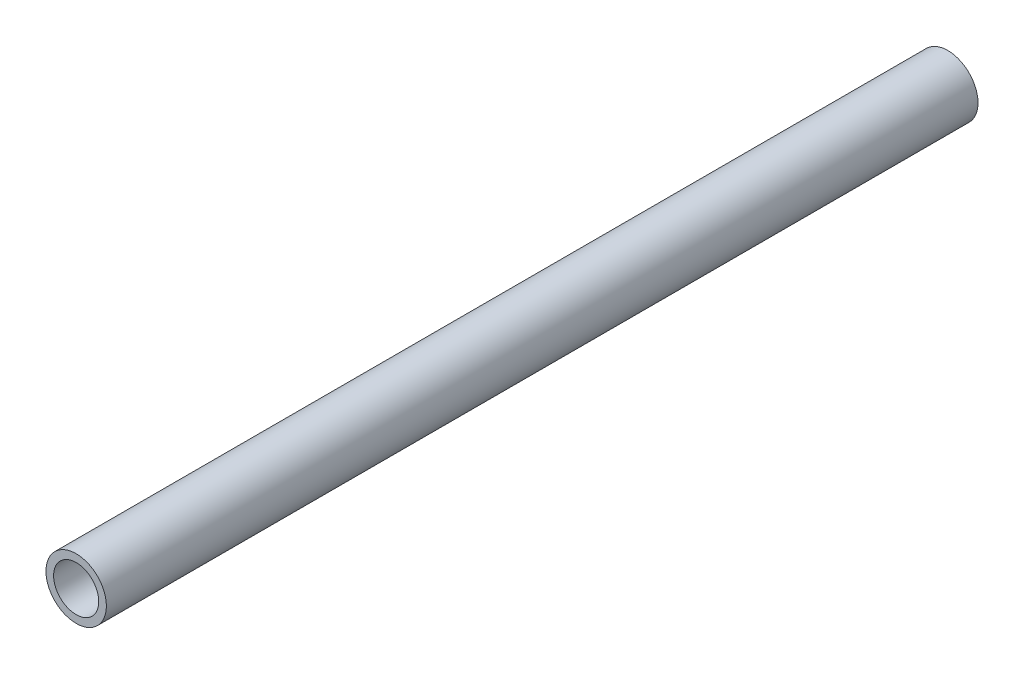
SolidWorks part; units mm, degrees
material "Ceramic Porcelain"
ref_plane "Front Plane" through (0, 0, 0) normal (0, 0, 1) x (1, 0, 0)
ref_plane "Top Plane" through (0, 0, 0) normal (0, 1, 0) x (1, 0, 0)
ref_plane "Right Plane" through (0, 0, 0) normal (1, 0, 0) x (0, 0, -1)
sketch "Sketch1" plane through (0, 0, 0) normal (0, 0, 1) x (1, 0, 0)
  circle A0 centre (0, 0) radius 2.125
  circle A1 centre (0, 0) radius 1.5875
  dimension "D1" = 4.25
  dimension "D2" = 3.175
extrude "Boss-Extrude1" add sketch "Sketch1" along normal blind 61.3
